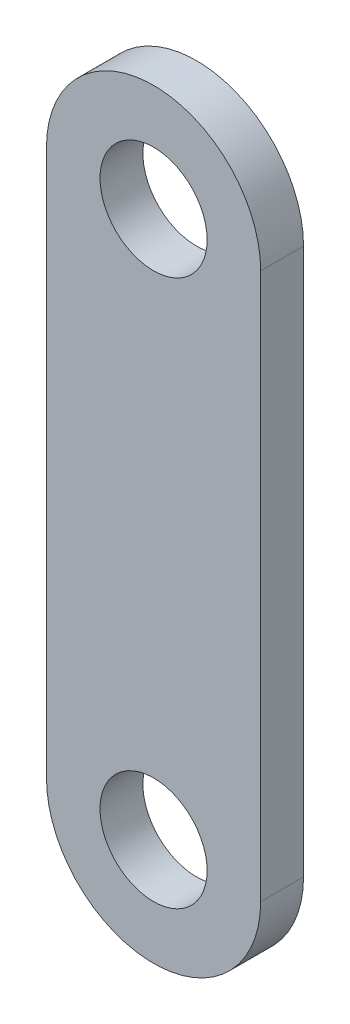
SolidWorks part; units mm, degrees
ref_plane "Front" through (0, 0, 0) normal (0, 0, 1) x (1, 0, 0)
ref_plane "Top" through (0, 0, 0) normal (0, 1, 0) x (1, 0, 0)
ref_plane "Right" through (0, 0, 0) normal (1, 0, 0) x (0, 0, -1)
sketch "Sketch1" plane through (0, 0, 0) normal (0, 0, 1) x (1, 0, 0)
  line L2 (50, -127.5) -> (50, 127.5)
  line L4 (-50, -127.5) -> (-50, 127.5)
  line L5 (50, -127.5) -> (-50, 127.5) construction
  line L6 (50, 127.5) -> (-50, -127.5) construction
  arc A0 (-50, 127.5) -> (50, 127.5) centre (0, 127.5) cw
  arc A1 (-50, -127.5) -> (50, -127.5) centre (0, -127.5) ccw
  point P0 (0, 0)
  point P6 (51.7544, 130.44)
  point P9 (0, 0)
  point P10 (0, 0)
  dimension "D1" = 100
  dimension "D2" = 255
extrude "Boss-Extrude1" add sketch "Sketch1" along normal blind 20
sketch "Sketch2" plane through (0, 0, 20) normal (0, 0, 1) x (1, 0, 0)
  circle A0 centre (0, 127.5) radius 25
  circle A1 centre (0, -127.5) radius 25
  dimension "D1" = 50
  dimension "D2" = 50
  dimension "D3" = 255
extrude "Cut-Extrude1" cut sketch "Sketch2" against normal blind 20
